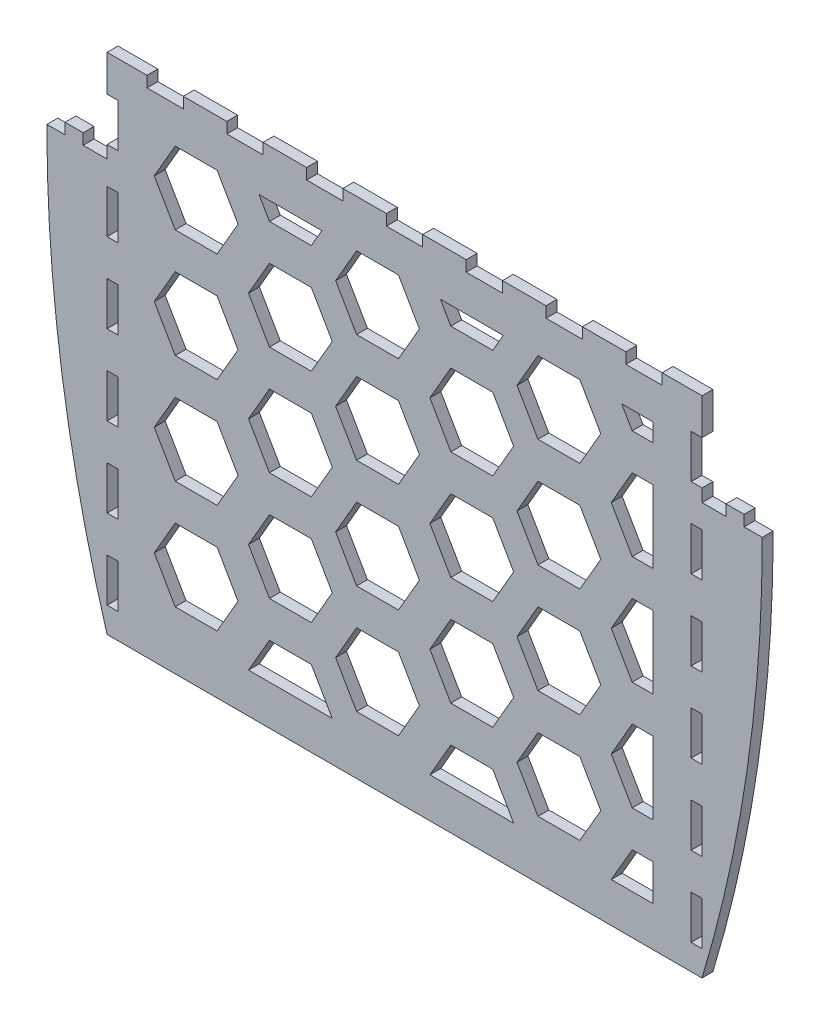
SolidWorks part; units mm, degrees
material "birch 3mm plywood"
ref_plane "Front Plane" through (0, 0, 0) normal (0, 0, 1) x (1, 0, 0)
ref_plane "Top Plane" through (0, 0, 0) normal (0, 1, 0) x (1, 0, 0)
ref_plane "Right Plane" through (0, 0, 0) normal (1, 0, 0) x (0, 0, -1)
sketch "Sketch1" plane through (0, 0, 152) normal (0, 0, 1) x (1, 0, 0)
  line L1 (-82, 69.5) -> (82, 69.5)
  line L2 (-82, 69.5) -> (-82, 44)
  line L3 (-82, -69.5) -> (82, -69.5)
  line L4 (82, 69.5) -> (82, 44)
  line L8 (-88.6, 47) -> (-93.6, 47)
  line L9 (-98.6, 44) -> (-98.6, 43.3771)
  line L12 (75, -62.5) -> (-75, -62.5) construction
  line L13 (75, 62.5) -> (75, -62.5) construction
  line L14 (-75, -62.5) -> (-75, 62.5) construction
  line L15 (-75, 62.5) -> (75, 62.5) construction
  line L33 (-93.6, 47) -> (-93.6, 44)
  line L34 (-93.6, 44) -> (-98.6, 44)
  line L35 (-88.6, 47) -> (-88.6, 44)
  line L36 (-88.6, 44) -> (-82, 44)
  line L37 (98.6, 44) -> (98.6, 43.3771)
  line L38 (93.6, 44) -> (98.6, 44)
  line L39 (93.6, 47) -> (93.6, 44)
  line L40 (88.6, 47) -> (93.6, 47)
  line L41 (88.6, 47) -> (88.6, 44)
  line L42 (88.6, 44) -> (82, 44)
  arc A12 (-98.6, 43.3771) -> (-82, -69.5) centre (293.4723, 43.3771) ccw
  arc A14 (98.6, 43.3771) -> (82, -69.5) centre (-293.4723, 43.3771) cw
  dimension "D3" = 7
  dimension "D11" = 150
  dimension "D12" = 125
  dimension "D13" = 7
  dimension "D14" = 22.5
  dimension "D15" = 16.6
  dimension "D16" = 3
  dimension "D17" = 5
  dimension "D18" = 5
extrude "Boss-Extrude1" add sketch "Sketch1" along normal blind 3
sketch "Sketch2" plane through (0, 0, 155) normal (0, 0, 1) x (1, 0, 0)
  line L0 (0, 69.5) -> (0, -69.5) construction
  line L1 (17, 69.5) -> (17, 66.5)
  line L2 (-5, 69.5) -> (5, 69.5)
  line L3 (-5, 69.5) -> (-5, 66.5)
  line L4 (-82, 69.5) -> (-82, 44)
  line L5 (-82, -69.5) -> (82, -69.5)
  line L6 (82, 44) -> (82, 69.5)
  line L7 (82, 69.5) -> (-82, 69.5)
  line L8 (-82, 69.5) -> (-82, 44)
  line L9 (-82, -69.5) -> (82, -69.5)
  line L10 (82, 44) -> (82, 69.5)
  line L11 (82, 69.5) -> (-82, 69.5)
  line L12 (-5, 66.5) -> (5, 66.5)
  line L13 (5, 69.5) -> (5, 66.5)
  line L14 (17, 69.5) -> (27, 69.5)
  line L15 (27, 69.5) -> (27, 66.5)
  line L16 (17, 66.5) -> (27, 66.5)
  line L17 (39, 69.5) -> (39, 66.5)
  line L18 (39, 69.5) -> (49, 69.5)
  line L19 (49, 69.5) -> (49, 66.5)
  line L20 (39, 66.5) -> (49, 66.5)
  line L21 (61, 69.5) -> (61, 66.5)
  line L22 (61, 69.5) -> (71, 69.5)
  line L23 (71, 69.5) -> (71, 66.5)
  line L24 (61, 66.5) -> (71, 66.5)
  line L25 (-27, 69.5) -> (-27, 66.5)
  line L26 (-27, 69.5) -> (-17, 69.5)
  line L27 (-17, 69.5) -> (-17, 66.5)
  line L28 (-27, 66.5) -> (-17, 66.5)
  line L29 (-49, 69.5) -> (-49, 66.5)
  line L30 (-49, 69.5) -> (-39, 69.5)
  line L31 (-39, 69.5) -> (-39, 66.5)
  line L32 (-49, 66.5) -> (-39, 66.5)
  line L33 (-71, 69.5) -> (-71, 66.5)
  line L34 (-71, 69.5) -> (-61, 69.5)
  line L35 (-61, 69.5) -> (-61, 66.5)
  line L36 (-71, 66.5) -> (-61, 66.5)
  line L37 (-82, 37.5) -> (-82, 25.5)
  line L38 (-82, 59.5) -> (-79, 59.5)
  line L39 (-82, 59.5) -> (-82, 47.5)
  line L40 (-82, 47.5) -> (-79, 47.5)
  line L41 (-79, 59.5) -> (-79, 47.5)
  line L42 (-82, 37.5) -> (-79, 37.5)
  line L43 (-79, 37.5) -> (-79, 25.5)
  line L44 (-82, 25.5) -> (-79, 25.5)
  line L45 (-82, 15.5) -> (-82, 3.5)
  line L46 (-82, 15.5) -> (-79, 15.5)
  line L47 (-79, 15.5) -> (-79, 3.5)
  line L48 (-82, 3.5) -> (-79, 3.5)
  line L49 (-82, -6.5) -> (-82, -18.5)
  line L50 (-82, -6.5) -> (-79, -6.5)
  line L51 (-79, -6.5) -> (-79, -18.5)
  line L52 (-82, -18.5) -> (-79, -18.5)
  line L53 (-82, -28.5) -> (-82, -40.5)
  line L54 (-82, -28.5) -> (-79, -28.5)
  line L55 (-79, -28.5) -> (-79, -40.5)
  line L56 (-82, -40.5) -> (-79, -40.5)
  line L57 (-82, -50.5) -> (-82, -62.5)
  line L58 (-82, -50.5) -> (-79, -50.5)
  line L59 (-79, -50.5) -> (-79, -62.5)
  line L60 (-82, -62.5) -> (-79, -62.5)
  line L65 (82, -50.5) -> (79, -50.5)
  line L66 (79, -50.5) -> (79, -62.5)
  line L67 (82, -62.5) -> (79, -62.5)
  line L68 (82, -50.5) -> (82, -62.5)
  line L69 (82, -28.5) -> (79, -28.5)
  line L70 (79, -28.5) -> (79, -40.5)
  line L71 (82, -40.5) -> (79, -40.5)
  line L72 (82, -28.5) -> (82, -40.5)
  line L73 (82, -6.5) -> (79, -6.5)
  line L74 (79, -6.5) -> (79, -18.5)
  line L75 (82, -18.5) -> (79, -18.5)
  line L76 (82, -6.5) -> (82, -18.5)
  line L77 (82, 15.5) -> (79, 15.5)
  line L78 (79, 15.5) -> (79, 3.5)
  line L79 (82, 3.5) -> (79, 3.5)
  line L80 (82, 15.5) -> (82, 3.5)
  line L81 (82, 37.5) -> (79, 37.5)
  line L82 (79, 37.5) -> (79, 25.5)
  line L83 (82, 25.5) -> (79, 25.5)
  line L84 (82, 37.5) -> (82, 25.5)
  line L85 (82, 47.5) -> (79, 47.5)
  line L86 (79, 59.5) -> (79, 47.5)
  line L87 (82, 59.5) -> (79, 59.5)
  line L88 (82, 59.5) -> (82, 47.5)
  line L97 (-88.6, 47) -> (-93.6, 47)
  line L98 (-88.6, 47) -> (-93.6, 47)
  line L99 (-98.6, 44) -> (-98.6, 43.3771)
  line L100 (-98.6, 44) -> (-98.6, 43.3771)
  line L101 (98.6, 43.3771) -> (98.6, 44)
  line L103 (98.6, 43.3771) -> (98.6, 44)
  line L109 (-82, 44) -> (-88.6, 44)
  line L110 (-82, 44) -> (-88.6, 44)
  line L111 (-88.6, 44) -> (-88.6, 47)
  line L112 (-88.6, 44) -> (-88.6, 47)
  line L113 (-93.6, 47) -> (-93.6, 44)
  line L114 (-93.6, 47) -> (-93.6, 44)
  line L115 (-93.6, 44) -> (-98.6, 44)
  line L116 (-93.6, 44) -> (-98.6, 44)
  line L121 (98.6, 44) -> (93.6, 44)
  line L122 (98.6, 44) -> (93.6, 44)
  line L123 (93.6, 44) -> (93.6, 47)
  line L124 (93.6, 44) -> (93.6, 47)
  line L125 (93.6, 47) -> (88.6, 47)
  line L126 (93.6, 47) -> (88.6, 47)
  line L127 (88.6, 47) -> (88.6, 44)
  line L128 (88.6, 47) -> (88.6, 44)
  line L129 (88.6, 44) -> (82, 44)
  line L130 (88.6, 44) -> (82, 44)
  arc A2 (-98.6, 43.3771) -> (-82, -69.5) centre (293.4723, 43.3771) ccw
  arc A3 (-98.6, 43.3771) -> (-82, -69.5) centre (293.4723, 43.3771) ccw
  arc A4 (82, -69.5) -> (98.6, 43.3771) centre (-293.4723, 43.3771) ccw
  arc A6 (82, -69.5) -> (98.6, 43.3771) centre (-293.4723, 43.3771) ccw
  point P10 (0, 66.5)
  line M64 (82, 44) -> (82, 69.5)
  line M65 (82, 69.5) -> (-82, 69.5)
  dimension "D2" = 10
  dimension "D3" = 3
  dimension "D6" = 12
  dimension "D7" = 12
  dimension "D8" = 3
  dimension "D9" = 12
  dimension "D10" = 10
  dimension "D12" = 10
  dimension "D1" = 0
  dimension "D4" = 4
  dimension "D5" = 4
  dimension "D11" = 6
extrude "Cut-Extrude1" cut sketch "Sketch2" against normal blind 10 contours L8 L44 L43 L42 | L33 L36 L35 L11 | L29 L32 L31 M65 | L25 L28 L27 L11 | L0 L12 L13 M65 | L0 L11 L3 L12 | L1 L16 L15 L11 | L17 L20 L19 L11 | L21 L24 L23 L11 | L87 L86 L85 M64 | L79 L77 L78 M64 | L75 L10 L73 L74 | L71 L69 L70 M64 | L67 L10 L65 L66 | L41 L40 L39 L38 | L47 L48 L45 L46 | L51 L52 L49 L50 | L55 L56 L53 L54 | L59 L60 L57 L58 | L82 L83 L84 L81
sketch "Sketch3" plane through (0, 0, 155) normal (0, 0, 1) x (1, 0, 0)
  line L0 (-49, 66.5) -> (-39, 66.5) construction
  line L1 (-45.906, 46.5) -> (-51.6795, 56.5)
  line L2 (-51.6795, 56.5) -> (-63.2265, 56.5)
  line L3 (-63.2265, 56.5) -> (-69, 46.5)
  line L4 (-69, 46.5) -> (-63.2265, 36.5)
  line L5 (-63.2265, 36.5) -> (-51.6795, 36.5)
  line L6 (-51.6795, 36.5) -> (-45.906, 46.5)
  line L7 (-79, 37.5) -> (-79, 25.5) construction
  line L8 (-19.9252, 31.5) -> (-25.6987, 41.5)
  line L9 (-25.6987, 41.5) -> (-37.2457, 41.5)
  line L10 (-37.2457, 41.5) -> (-43.0192, 31.5)
  line L11 (-43.0192, 31.5) -> (-37.2457, 21.5)
  line L12 (-37.2457, 21.5) -> (-25.6987, 21.5)
  line L13 (-25.6987, 21.5) -> (-19.9252, 31.5)
  line L14 (4.094, 46.5) -> (-1.6795, 56.5)
  line L15 (-1.6795, 56.5) -> (-13.2265, 56.5)
  line L16 (-13.2265, 56.5) -> (-19, 46.5)
  line L17 (-19, 46.5) -> (-13.2265, 36.5)
  line L18 (-13.2265, 36.5) -> (-1.6795, 36.5)
  line L19 (-1.6795, 36.5) -> (4.094, 46.5)
  line L20 (30.0748, 31.5) -> (24.3013, 41.5)
  line L21 (24.3013, 41.5) -> (12.7543, 41.5)
  line L22 (12.7543, 41.5) -> (6.9808, 31.5)
  line L23 (6.9808, 31.5) -> (12.7543, 21.5)
  line L24 (12.7543, 21.5) -> (24.3013, 21.5)
  line L25 (24.3013, 21.5) -> (30.0748, 31.5)
  line L26 (54.094, 46.5) -> (48.3205, 56.5)
  line L27 (48.3205, 56.5) -> (36.7735, 56.5)
  line L28 (36.7735, 56.5) -> (31, 46.5)
  line L29 (31, 46.5) -> (36.7735, 36.5)
  line L30 (36.7735, 36.5) -> (48.3205, 36.5)
  line L31 (48.3205, 36.5) -> (54.094, 46.5)
  line L33 (68.5278, 41.5) -> (62.7543, 41.5)
  line L34 (62.7543, 41.5) -> (56.9808, 31.5)
  line L35 (56.9808, 31.5) -> (62.7543, 21.5)
  line L36 (62.7543, 21.5) -> (68.5278, 21.5)
  line L38 (4.094, 16.5) -> (-1.6795, 26.5)
  line L39 (-1.6795, 26.5) -> (-13.2265, 26.5)
  line L40 (-13.2265, 26.5) -> (-19, 16.5)
  line L41 (-19, 16.5) -> (-13.2265, 6.5)
  line L42 (-13.2265, 6.5) -> (-1.6795, 6.5)
  line L43 (-1.6795, 6.5) -> (4.094, 16.5)
  line L44 (30.0748, 1.5) -> (24.3013, 11.5)
  line L45 (24.3013, 11.5) -> (12.7543, 11.5)
  line L46 (12.7543, 11.5) -> (6.9808, 1.5)
  line L47 (6.9808, 1.5) -> (12.7543, -8.5)
  line L48 (12.7543, -8.5) -> (24.3013, -8.5)
  line L49 (24.3013, -8.5) -> (30.0748, 1.5)
  line L50 (54.094, 16.5) -> (48.3205, 26.5)
  line L51 (48.3205, 26.5) -> (36.7735, 26.5)
  line L52 (36.7735, 26.5) -> (31, 16.5)
  line L53 (31, 16.5) -> (36.7735, 6.5)
  line L54 (36.7735, 6.5) -> (48.3205, 6.5)
  line L55 (48.3205, 6.5) -> (54.094, 16.5)
  line L57 (68.5278, 11.5) -> (62.7543, 11.5)
  line L58 (62.7543, 11.5) -> (56.9808, 1.5)
  line L59 (56.9808, 1.5) -> (62.7543, -8.5)
  line L60 (62.7543, -8.5) -> (68.5278, -8.5)
  line L62 (4.094, -13.5) -> (-1.6795, -3.5)
  line L63 (-1.6795, -3.5) -> (-13.2265, -3.5)
  line L64 (-13.2265, -3.5) -> (-19, -13.5)
  line L65 (-19, -13.5) -> (-13.2265, -23.5)
  line L66 (-13.2265, -23.5) -> (-1.6795, -23.5)
  line L67 (-1.6795, -23.5) -> (4.094, -13.5)
  line L68 (30.0748, -28.5) -> (24.3013, -18.5)
  line L69 (24.3013, -18.5) -> (12.7543, -18.5)
  line L70 (12.7543, -18.5) -> (6.9808, -28.5)
  line L71 (6.9808, -28.5) -> (12.7543, -38.5)
  line L72 (12.7543, -38.5) -> (24.3013, -38.5)
  line L73 (24.3013, -38.5) -> (30.0748, -28.5)
  line L74 (54.094, -13.5) -> (48.3205, -3.5)
  line L75 (48.3205, -3.5) -> (36.7735, -3.5)
  line L76 (36.7735, -3.5) -> (31, -13.5)
  line L77 (31, -13.5) -> (36.7735, -23.5)
  line L78 (36.7735, -23.5) -> (48.3205, -23.5)
  line L79 (48.3205, -23.5) -> (54.094, -13.5)
  line L81 (68.5278, -18.5) -> (62.7543, -18.5)
  line L82 (62.7543, -18.5) -> (56.9808, -28.5)
  line L83 (56.9808, -28.5) -> (62.7543, -38.5)
  line L84 (62.7543, -38.5) -> (68.5278, -38.5)
  line L86 (4.094, -43.5) -> (-1.6795, -33.5)
  line L87 (-1.6795, -33.5) -> (-13.2265, -33.5)
  line L88 (-13.2265, -33.5) -> (-19, -43.5)
  line L89 (-19, -43.5) -> (-13.2265, -53.5)
  line L90 (-13.2265, -53.5) -> (-1.6795, -53.5)
  line L91 (-1.6795, -53.5) -> (4.094, -43.5)
  line L92 (30.0748, -58.5) -> (24.3013, -48.5)
  line L93 (24.3013, -48.5) -> (12.7543, -48.5)
  line L94 (12.7543, -48.5) -> (6.9808, -58.5)
  line L98 (54.094, -43.5) -> (48.3205, -33.5)
  line L99 (48.3205, -33.5) -> (36.7735, -33.5)
  line L100 (36.7735, -33.5) -> (31, -43.5)
  line L101 (31, -43.5) -> (36.7735, -53.5)
  line L102 (36.7735, -53.5) -> (48.3205, -53.5)
  line L103 (48.3205, -53.5) -> (54.094, -43.5)
  line L105 (68.5278, -48.5) -> (62.7543, -48.5)
  line L106 (62.7543, -48.5) -> (56.9808, -58.5)
  line L134 (-45.906, 16.5) -> (-51.6795, 26.5)
  line L135 (-51.6795, 26.5) -> (-63.2265, 26.5)
  line L136 (-63.2265, 26.5) -> (-69, 16.5)
  line L137 (-69, 16.5) -> (-63.2265, 6.5)
  line L138 (-63.2265, 6.5) -> (-51.6795, 6.5)
  line L139 (-51.6795, 6.5) -> (-45.906, 16.5)
  line L140 (-19.9252, 1.5) -> (-25.6987, 11.5)
  line L141 (-25.6987, 11.5) -> (-37.2457, 11.5)
  line L142 (-37.2457, 11.5) -> (-43.0192, 1.5)
  line L143 (-43.0192, 1.5) -> (-37.2457, -8.5)
  line L144 (-37.2457, -8.5) -> (-25.6987, -8.5)
  line L145 (-25.6987, -8.5) -> (-19.9252, 1.5)
  line L146 (-45.906, -13.5) -> (-51.6795, -3.5)
  line L147 (-51.6795, -3.5) -> (-63.2265, -3.5)
  line L148 (-63.2265, -3.5) -> (-69, -13.5)
  line L149 (-69, -13.5) -> (-63.2265, -23.5)
  line L150 (-63.2265, -23.5) -> (-51.6795, -23.5)
  line L151 (-51.6795, -23.5) -> (-45.906, -13.5)
  line L152 (-19.9252, -28.5) -> (-25.6987, -18.5)
  line L153 (-25.6987, -18.5) -> (-37.2457, -18.5)
  line L154 (-37.2457, -18.5) -> (-43.0192, -28.5)
  line L155 (-43.0192, -28.5) -> (-37.2457, -38.5)
  line L156 (-37.2457, -38.5) -> (-25.6987, -38.5)
  line L157 (-25.6987, -38.5) -> (-19.9252, -28.5)
  line L158 (-45.906, -43.5) -> (-51.6795, -33.5)
  line L159 (-51.6795, -33.5) -> (-63.2265, -33.5)
  line L160 (-63.2265, -33.5) -> (-69, -43.5)
  line L161 (-69, -43.5) -> (-63.2265, -53.5)
  line L162 (-63.2265, -53.5) -> (-51.6795, -53.5)
  line L163 (-51.6795, -53.5) -> (-45.906, -43.5)
  line L164 (-19.9252, -58.5) -> (-25.6987, -48.5)
  line L165 (-25.6987, -48.5) -> (-37.2457, -48.5)
  line L166 (-37.2457, -48.5) -> (-43.0192, -58.5)
  line L185 (-40.1325, 56.5) -> (-37.2457, 51.5)
  line L186 (-37.2457, 51.5) -> (-25.6987, 51.5)
  line L187 (-25.6987, 51.5) -> (-22.812, 56.5)
  line L188 (31, -73.5) -> (36.7735, -83.5) [skipped]
  line L189 (36.7735, -83.5) -> (48.3205, -83.5) [skipped]
  line L190 (48.3205, -83.5) -> (54.094, -73.5) [skipped]
  line L191 (80.0748, -88.5) -> (74.3013, -78.5) [skipped]
  line L192 (74.3013, -78.5) -> (62.7543, -78.5) [skipped]
  line L193 (62.7543, -78.5) -> (56.9808, -88.5) [skipped]
  line L194 (56.9808, -88.5) -> (62.7543, -98.5) [skipped]
  line L195 (62.7543, -98.5) -> (74.3013, -98.5) [skipped]
  line L196 (74.3013, -98.5) -> (80.0748, -88.5) [skipped]
  line L197 (54.094, -73.5) -> (48.3205, -63.5) [skipped]
  line L198 (48.3205, -63.5) -> (36.7735, -63.5) [skipped]
  line L199 (36.7735, -63.5) -> (31, -73.5) [skipped]
  line L200 (-1.6795, -83.5) -> (4.094, -73.5) [skipped]
  line L201 (30.0748, -88.5) -> (24.3013, -78.5) [skipped]
  line L202 (24.3013, -78.5) -> (12.7543, -78.5) [skipped]
  line L203 (12.7543, -78.5) -> (6.9808, -88.5) [skipped]
  line L204 (6.9808, -88.5) -> (12.7543, -98.5) [skipped]
  line L205 (12.7543, -98.5) -> (24.3013, -98.5) [skipped]
  line L206 (24.3013, -98.5) -> (30.0748, -88.5) [skipped]
  line L207 (4.094, -73.5) -> (-1.6795, -63.5) [skipped]
  line L208 (-1.6795, -63.5) -> (-13.2265, -63.5) [skipped]
  line L209 (-13.2265, -63.5) -> (-19, -73.5) [skipped]
  line L210 (-19, -73.5) -> (-13.2265, -83.5) [skipped]
  line L211 (-13.2265, -83.5) -> (-1.6795, -83.5) [skipped]
  line L212 (-19.9252, -88.5) -> (-25.6987, -78.5) [skipped]
  line L213 (-25.6987, -78.5) -> (-37.2457, -78.5) [skipped]
  line L214 (-37.2457, -78.5) -> (-43.0192, -88.5) [skipped]
  line L215 (-43.0192, -88.5) -> (-37.2457, -98.5) [skipped]
  line L216 (-37.2457, -98.5) -> (-25.6987, -98.5) [skipped]
  line L217 (-25.6987, -98.5) -> (-19.9252, -88.5) [skipped]
  line L218 (-45.906, -73.5) -> (-51.6795, -63.5) [skipped]
  line L219 (-51.6795, -63.5) -> (-63.2265, -63.5) [skipped]
  line L220 (-63.2265, -63.5) -> (-69, -73.5) [skipped]
  line L221 (-69, -73.5) -> (-63.2265, -83.5) [skipped]
  line L222 (-63.2265, -83.5) -> (-51.6795, -83.5) [skipped]
  line L223 (-51.6795, -83.5) -> (-45.906, -73.5) [skipped]
  line L224 (-40.1325, 56.5) -> (-22.812, 56.5)
  line L225 (24.3013, 51.5) -> (27.188, 56.5)
  line L226 (-25.6987, 71.5) -> (-37.2457, 71.5) [skipped]
  line L227 (-19.9252, 61.5) -> (-25.6987, 71.5) [skipped]
  line L228 (-37.2457, 71.5) -> (-43.0192, 61.5) [skipped]
  line L229 (9.8675, 56.5) -> (27.188, 56.5)
  line L230 (12.7543, 51.5) -> (24.3013, 51.5)
  line L231 (9.8675, 56.5) -> (12.7543, 51.5)
  line L233 (59.8675, 56.5) -> (68.5278, 56.5)
  line L234 (62.7543, 51.5) -> (68.5278, 51.5)
  line L235 (59.8675, 56.5) -> (62.7543, 51.5)
  line L236 (68.5278, 56.5) -> (68.5278, 51.5)
  line L237 (68.5278, 41.5) -> (68.5278, 21.5)
  line L238 (68.5278, 11.5) -> (68.5278, -8.5)
  line L239 (68.5278, -18.5) -> (68.5278, -38.5)
  line L240 (68.5278, -48.5) -> (68.5278, -58.5)
  line L241 (56.9808, -58.5) -> (68.5278, -58.5)
  line L242 (6.9808, -58.5) -> (30.0748, -58.5)
  line L243 (-43.0192, -58.5) -> (-19.9252, -58.5)
  line L245 (74.3013, 51.5) -> (77.188, 56.5) [skipped]
  line L246 (80.0748, -58.5) -> (74.3013, -48.5) [skipped]
  line L247 (74.3013, -68.5) -> (80.0748, -58.5) [skipped]
  line L248 (62.7543, -68.5) -> (74.3013, -68.5) [skipped]
  line L249 (56.9808, -58.5) -> (62.7543, -68.5) [skipped]
  line L250 (74.3013, -38.5) -> (80.0748, -28.5) [skipped]
  line L251 (80.0748, -28.5) -> (74.3013, -18.5) [skipped]
  line L252 (74.3013, -8.5) -> (80.0748, 1.5) [skipped]
  line L253 (80.0748, 1.5) -> (74.3013, 11.5) [skipped]
  line L254 (80.0748, 31.5) -> (74.3013, 41.5) [skipped]
  line L255 (74.3013, 21.5) -> (80.0748, 31.5) [skipped]
  line L256 (6.9808, -58.5) -> (12.7543, -68.5) [skipped]
  line L257 (12.7543, -68.5) -> (24.3013, -68.5) [skipped]
  line L258 (24.3013, -68.5) -> (30.0748, -58.5) [skipped]
  line L259 (-25.6987, -68.5) -> (-19.9252, -58.5) [skipped]
  line L260 (-43.0192, -58.5) -> (-37.2457, -68.5) [skipped]
  line L261 (-37.2457, -68.5) -> (-25.6987, -68.5) [skipped]
  circle A0 centre (-57.453, 46.5) radius 10 construction
  circle A1 centre (-31.4722, 31.5) radius 10 construction
  circle A2 centre (-7.453, 46.5) radius 10 construction
  circle A3 centre (18.5278, 31.5) radius 10 construction
  circle A4 centre (42.547, 46.5) radius 10 construction
  circle A5 centre (68.5278, 31.5) radius 10 construction
  circle A6 centre (-7.453, 16.5) radius 10 construction
  circle A7 centre (18.5278, 1.5) radius 10 construction
  circle A8 centre (42.547, 16.5) radius 10 construction
  circle A9 centre (68.5278, 1.5) radius 10 construction
  circle A10 centre (-7.453, -13.5) radius 10 construction
  circle A11 centre (18.5278, -28.5) radius 10 construction
  circle A12 centre (42.547, -13.5) radius 10 construction
  circle A13 centre (68.5278, -28.5) radius 10 construction
  circle A14 centre (-7.453, -43.5) radius 10 construction
  circle A15 centre (18.5278, -58.5) radius 10 construction
  circle A16 centre (42.547, -43.5) radius 10 construction
  circle A17 centre (68.5278, -58.5) radius 10 construction
  circle A18 centre (18.5278, 61.5) radius 10 construction
  circle A19 centre (68.5278, 61.5) radius 10 construction
  circle A22 centre (-57.453, 16.5) radius 10 construction
  circle A23 centre (-31.4722, 1.5) radius 10 construction
  circle A24 centre (-57.453, -13.5) radius 10 construction
  circle A25 centre (-31.4722, -28.5) radius 10 construction
  circle A26 centre (-57.453, -43.5) radius 10 construction
  circle A27 centre (-31.4722, -58.5) radius 10 construction
  circle A30 centre (-31.4722, 61.5) radius 10 construction
  circle A31 centre (42.547, -73.5) radius 10 construction
  circle A32 centre (68.5278, -88.5) radius 10 construction
  circle A33 centre (-7.453, -73.5) radius 10 construction
  circle A34 centre (18.5278, -88.5) radius 10 construction
  circle A35 centre (-31.4722, -88.5) radius 10 construction
  circle A36 centre (-57.453, -73.5) radius 10 construction
  dimension "D3" = 20
  dimension "D1" = 10
  dimension "D2" = 10
  dimension "D4" = 2
  dimension "D5" = 3
  dimension "D6" = 5
  dimension "D7" = 2
  dimension "D8" = 3
extrude "Cut-Extrude2" cut sketch "Sketch3" against normal through all
